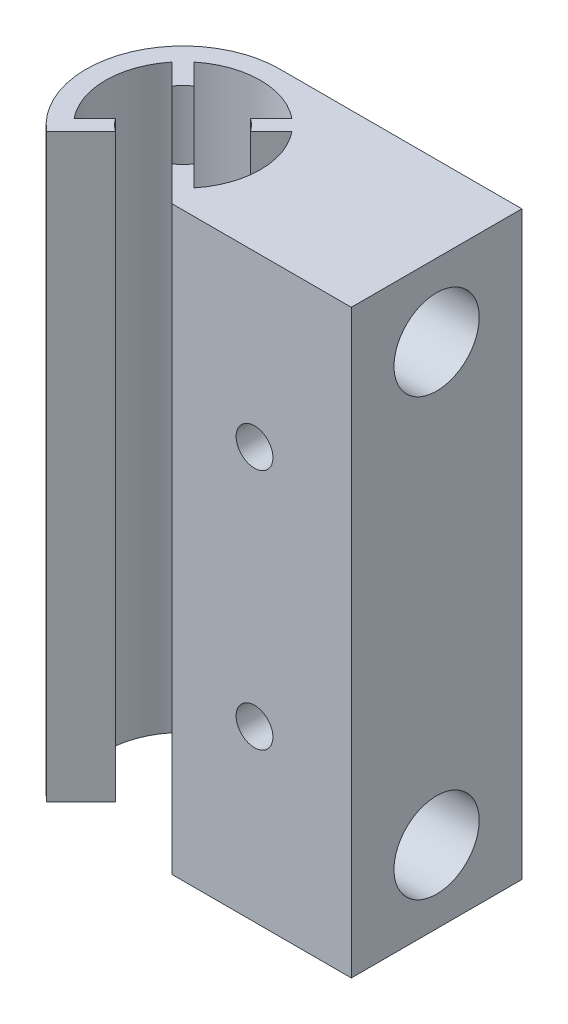
SolidWorks part; units mm, degrees
material "ABS"
ref_plane "Front Plane" through (0, 0, 0) normal (0, 0, 1) x (1, 0, 0)
ref_plane "Top Plane" through (0, 0, 0) normal (0, 1, 0) x (1, 0, 0)
ref_plane "Right Plane" through (0, 0, 0) normal (1, 0, 0) x (0, 0, -1)
sketch "Sketch1" plane through (0, 0, 0) normal (0, 1, 0) x (1, 0, 0)
  line L0 (0, 10) -> (-10, 10)
  line L1 (-3.5173, -7.6141) -> (15, -7.6141)
  line L2 (0, 10) -> (15, 10)
  line L5 (15, 1.193) -> (15, 10)
  line L6 (15, 1.193) -> (15, -7.6141)
  line L14 (-15.0628, 6.1942) -> (-12.9243, 4.0557)
  line L16 (-14.0557, -2.9243) -> (-16.1942, -5.0628)
  line L19 (-7.0757, -4.0557) -> (-3.5173, -7.6141)
  line L20 (-5.9443, 2.9243) -> (-3.8058, 5.0628)
  line L21 (-14.0557, 2.9243) -> (-16.1942, 5.0628)
  line L22 (-12.9243, -4.0557) -> (-16.4827, -7.6141)
  line L23 (-5.9443, -2.9243) -> (-3.8058, -5.0628)
  line L24 (-7.0757, 4.0557) -> (-4.9372, 6.1942)
  arc A0 (-14.0557, -2.9243) -> (-12.9243, -4.0557) centre (-10, 0) ccw
  arc A1 (-10, 10) -> (-16.4827, -7.6141) centre (-10, 0) ccw
  arc A2 (-4.9372, 6.1942) -> (-15.0628, 6.1942) centre (-10, 0) ccw
  arc A3 (-7.0757, -4.0557) -> (-5.9443, -2.9243) centre (-10, 0) ccw
  arc A4 (-5.9443, 2.9243) -> (-7.0757, 4.0557) centre (-10, 0) ccw
  arc A5 (-12.9243, 4.0557) -> (-14.0557, 2.9243) centre (-10, 0) ccw
  arc A6 (-16.1942, 5.0628) -> (-16.1942, -5.0628) centre (-10, 0) ccw
  arc A9 (-3.8058, -5.0628) -> (-3.8058, 5.0628) centre (-10, 0) ccw
extrude "Boss-Extrude1" add sketch "Sketch1" along normal blind 60
sketch "Sketch3" plane through (0, 0, -10) normal (0, 0, -1) x (-1, 0, 0)
  circle A2 centre (-5, 42.5) radius 1.9
  circle A3 centre (-5, 17.5) radius 1.9
extrude "Cut-Extrude2" cut sketch "Sketch3" against normal up to next
sketch "Sketch4" plane through (15, 0, 0) normal (1, 0, 0) x (0, 0, -1)
  circle A0 centre (1.193, 7.5) radius 4.4
  circle A1 centre (1.193, 52.5) radius 4.4
extrude "Cut-Extrude3" cut sketch "Sketch4" against normal blind 10
